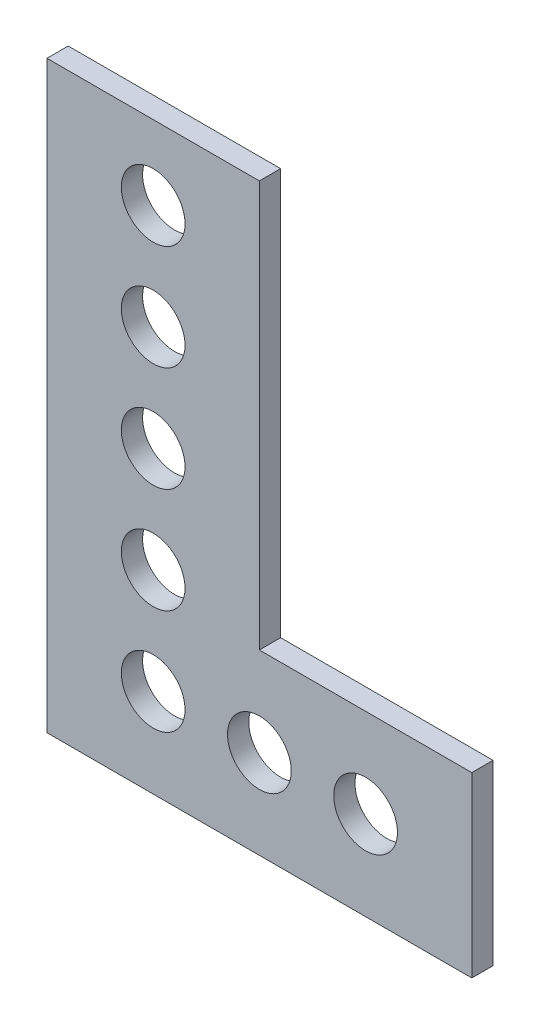
SolidWorks part; units mm, degrees
ref_plane "Front Plane" through (0, 0, 0) normal (0, 0, 1) x (1, 0, 0)
ref_plane "Top Plane" through (0, 0, 0) normal (0, 1, 0) x (1, 0, 0)
ref_plane "Right Plane" through (0, 0, 0) normal (1, 0, 0) x (0, 0, -1)
sketch "Sketch1" plane through (0, 0, 0) normal (0, 0, 1) x (1, 0, 0)
  line L0 (-20, 55) -> (-20, 0)
  line L1 (-20, 0) -> (20, 0)
  line L2 (20, 0) -> (20, 16.75)
  line L3 (20, 16.75) -> (0, 16.75)
  line L4 (0, 16.75) -> (0, 55)
  line L5 (0, 55) -> (-20, 55)
  line L6 (-10, 55) -> (-10, 0) construction
  line L7 (20, 8.375) -> (-20, 8.375) construction
  circle A0 centre (-10, 48) radius 3
  circle A1 centre (10, 8.375) radius 3
  circle A2 centre (-10, 38.0938) radius 3
  circle A3 centre (-10, 28.1875) radius 3
  circle A4 centre (-10, 18.2813) radius 3
  circle A5 centre (-10, 8.375) radius 3
  circle A6 centre (0, 8.375) radius 3
  point P6 (0, 0)
  point P26 (12.0655, 8.375)
  point P27 (10, 16.75)
  dimension "D5" = 6
  dimension "D6" = 6
  dimension "D8" = 7
  dimension "D9" = 6
  dimension "D1" = 40
  dimension "D2" = 55
  dimension "D3" = 20
  dimension "D4" = 16.75
  dimension "D7" = 5
extrude "Boss-Extrude1" add sketch "Sketch1" along normal blind 2
